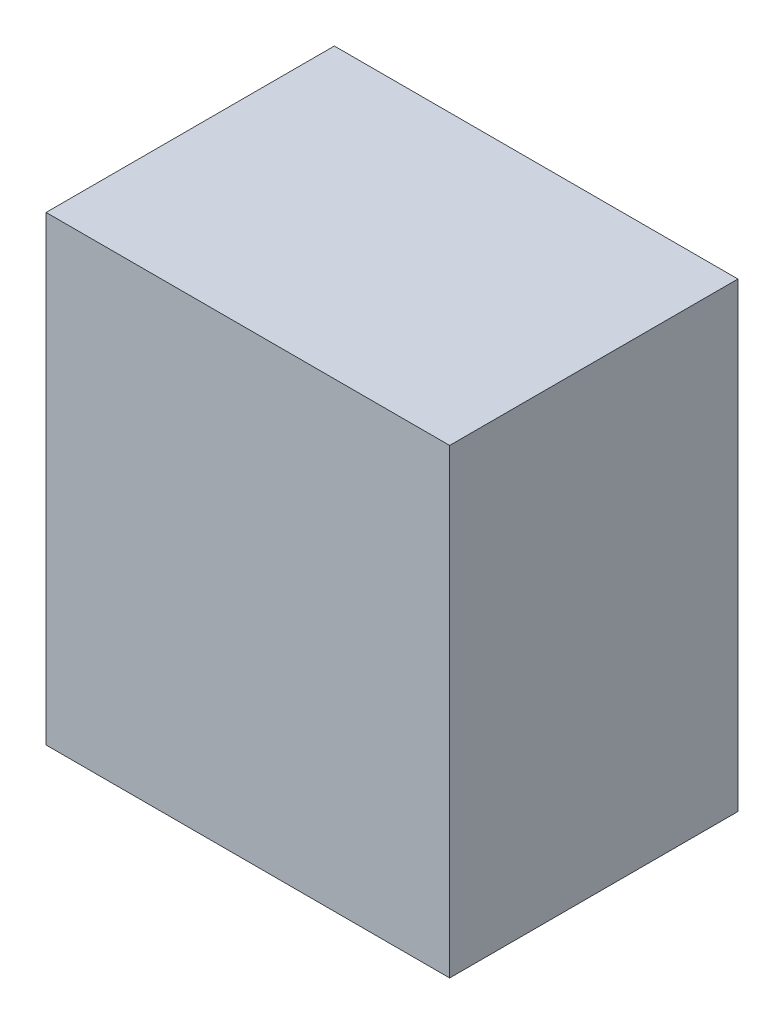
SolidWorks part; units mm, degrees
material "1023 al carbonio, lamiera (SS)"
ref_plane "Piano frontale" through (0, 0, 0) normal (0, 0, 1) x (1, 0, 0)
ref_plane "Piano superiore" through (0, 0, 0) normal (0, 1, 0) x (1, 0, 0)
ref_plane "Piano destro" through (0, 0, 0) normal (1, 0, 0) x (0, 0, -1)
sketch "Schizzo1" plane through (0, 0, 0) normal (0, 0, 1) x (1, 0, 0)
  line L0 (17.5, 40) -> (17.5, 0) construction
  line L1 (0, 0) -> (35, 0)
  line L2 (0, 0) -> (0, 40)
  line L3 (0, 40) -> (35, 40)
  line L4 (35, 0) -> (35, 40)
  dimension "D1" = 40
  dimension "D2" = 35
extrude "Estrusione-Estrusione1" add sketch "Schizzo1" along normal blind 25
